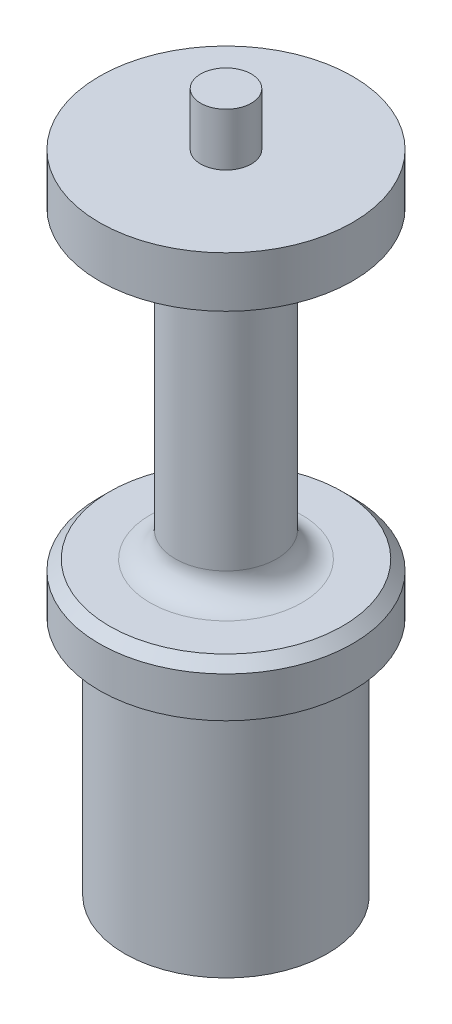
SolidWorks part; units mm, degrees
material "6061 Alloy"
ref_plane "Front Plane" through (0, 0, 0) normal (0, 0, 1) x (1, 0, 0)
ref_plane "Top Plane" through (0, 0, 0) normal (0, 1, 0) x (1, 0, 0)
ref_plane "Right Plane" through (0, 0, 0) normal (1, 0, 0) x (0, 0, -1)
sketch "Sketch1" plane through (0, 0, 0) normal (0, 1, 0) x (1, 0, 0)
  circle A0 centre (0, 0) radius 12.7
  dimension "D1" = 25.4
extrude "Boss-Extrude1" add sketch "Sketch1" along normal blind 30.1625
sketch "Sketch4" plane through (0, 30.1625, 0) normal (0, 1, 0) x (1, 0, 0)
  circle A0 centre (0, 0) radius 15.875
  dimension "D1" = 31.75
extrude "Boss-Extrude2" add sketch "Sketch4" along normal blind 50.8 contours A0
sketch "Sketch2" plane through (0, 0, 0) normal (0, -1, 0) x (1, 0, 0)
  line L0 (-8.777, 1.1225) -> (-1.1225, 8.777)
  line L1 (-5.4125, -7) -> (5.4125, -7)
  line L2 (-7, -5.4125) -> (-7, 5.4125)
  line L3 (-5.4125, 7) -> (5.4125, 7)
  line L4 (7, -5.4125) -> (7, 5.4125)
  line L5 (-7, -7) -> (7, 7) construction
  line L6 (-7, 7) -> (7, -7) construction
  line L7 (-8.777, -1.1225) -> (-1.1225, -8.777)
  line L8 (1.1225, 8.777) -> (8.777, 1.1225)
  line L9 (1.1225, -8.777) -> (8.777, -1.1225)
  line L10 (-9.8995, 0) -> (9.8995, 0) construction
  line L11 (0, 9.8995) -> (0, -9.8995) construction
  circle A0 centre (0, 0) radius 9 construction
  arc A1 (-8.777, 1.1225) -> (-8.777, -1.1225) centre (-7.6544, 0) ccw
  arc A2 (-7, -5.4125) -> (-5.4125, -7) centre (-5.4125, -5.4125) ccw
  arc A3 (-1.1225, -8.777) -> (1.1225, -8.777) centre (0, -7.6544) ccw
  arc A4 (5.4125, -7) -> (7, -5.4125) centre (5.4125, -5.4125) ccw
  arc A5 (8.777, -1.1225) -> (8.777, 1.1225) centre (7.6544, 0) ccw
  arc A6 (7, 5.4125) -> (5.4125, 7) centre (5.4125, 5.4125) ccw
  arc A7 (1.1225, 8.777) -> (-1.1225, 8.777) centre (0, 7.6544) ccw
  arc A8 (-5.4125, 7) -> (-7, 5.4125) centre (-5.4125, 5.4125) ccw
  point P0 (0, 0)
  point P7 (0, 0)
  dimension "D2" = 18
  dimension "D3" = 1.5875
  dimension "D1" = 14
extrude "Cut-Extrude1" cut sketch "Sketch2" against normal blind 11.176 contours L0 A1 L7 L2 | L1 L9 L4 L8 L3 L0 L2 L7 | L3 A8 L2 L0 | L8 A7 L0 L3 | L4 A6 L3 L8 | L9 A5 L8 L4 | L1 A4 L4 L9 | L7 A3 L9 L1 | L2 A2 L1 L7
sketch "Sketch3" plane through (0, 11.176, 0) normal (0, -1, 0) x (1, 0, 0)
  circle A0 centre (0, 0) radius 6
  dimension "D1" = 12
extrude "Cut-Extrude2" cut sketch "Sketch3" against normal blind 8
sketch "Sketch5" plane through (0, 80.9625, 0) normal (0, 1, 0) x (1, 0, 0)
  circle A0 centre (0, 0) radius 3.175
  dimension "D1" = 6.35
extrude "Boss-Extrude3" add sketch "Sketch5" along normal blind 6.604
hole_wizard "#8-32 Tapped Hole1" [suppressed] positions "Sketch6" profile "Sketch8" tap size "#8-32" standard "ANSI Inch"
sketch "Sketch6" plane through (0, 87.5665, 0) normal (0, 1, 0) x (1, 0, 0)
  point P0 (0, 0)
sketch "Sketch8" plane through (0, 87.5665, 0) normal (1, 0, 0) x (0, 0, 1)
  line L0 (0, 0) -> (0, 87.5665)
  line L1 (0, 87.5665) -> (1.7272, 87.5665)
  line L2 (1.7272, 87.5665) -> (1.7272, 0)
  line L5 (1.7272, 0) -> (0, 0)
  line L11 (0, -6.35) -> (0, 107.95) construction
  dimension "Thru Tap Drill Dia." = 3.4544
  dimension "Thru Tap Drill Depth" = 87.5665
cosmetic thread "Hole Thread1" [suppressed] parameters "D2"=4.1656
sketch "Sketch9" plane through (0, 80.9625, 0) normal (0, 1, 0) x (1, 0, 0)
  circle A0 centre (0, 0) radius 15.875 construction
  circle A1 centre (0, 0) radius 15.875
  circle A2 centre (0, 0) radius 6.35
  dimension "D1" = 12.7
extrude "Cut-Extrude3" cut sketch "Sketch9" against normal blind 38.1 from offset 6.35 offset against normal yes
fillet "Fillet1" radius 3.175 2 edges at (0, 74.6125, 6.35) (0, 36.5125, 6.35)
chamfer "Chamfer1" distance 1.27 angle 45 1 edges at (0, 36.5125, 15.875)
